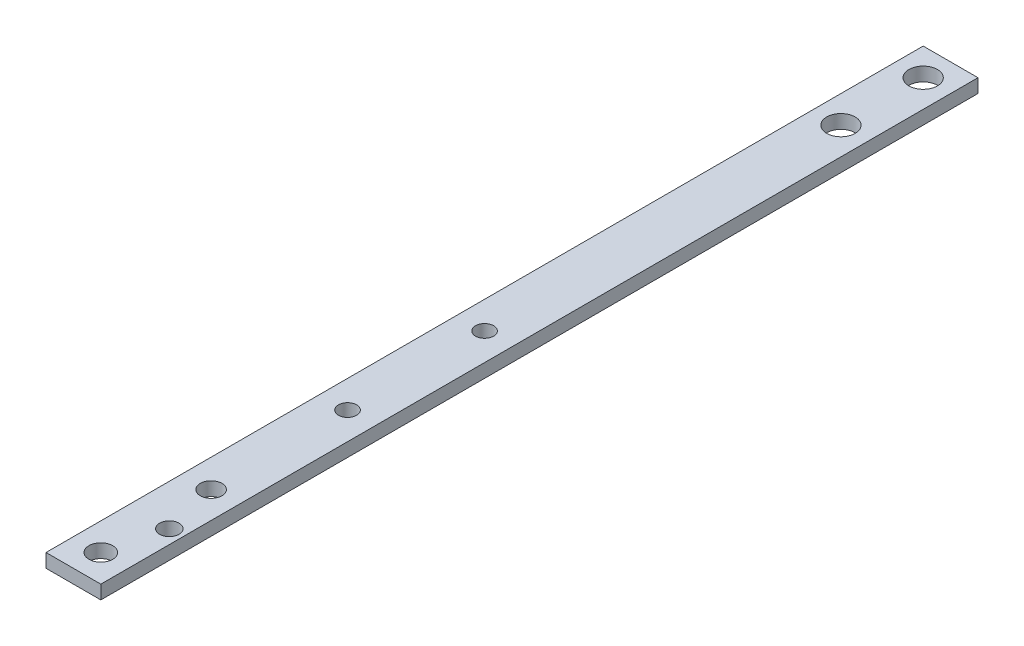
SolidWorks part; units mm, degrees
material "Copper"
ref_plane "Front Plane" through (0, 0, 0) normal (0, 0, 1) x (1, 0, 0)
ref_plane "Top Plane" through (0, 0, 0) normal (0, 1, 0) x (1, 0, 0)
ref_plane "Right Plane" through (0, 0, 0) normal (1, 0, 0) x (0, 0, -1)
sketch "Sketch1" plane through (0, 0, 0) normal (0, 0, 1) x (1, 0, 0)
  line L1 (0, 0) -> (12.7, 0)
  line L2 (0, 0) -> (0, 3.175)
  line L3 (0, 3.175) -> (12.7, 3.175)
  line L4 (12.7, 0) -> (12.7, 3.175)
  dimension "D1" = 12.7
  dimension "D2" = 3.175
extrude "Boss-Extrude1" add sketch "Sketch1" along normal blind 203.2
hole_wizard "M6 Clearance Hole1" positions "Sketch3" profile "Sketch2" hole size "M6" standard "ANSI Metric" end condition through all
sketch "Sketch3" plane through (0, 0, 0) normal (0, -1, 0) x (-1, 0, 0)
  line L0 (0, 0) -> (-12.7, 0) construction
  point P0 (-6.35, -6.35)
  point P5 (-6.35, 0)
  point P6 (-6.35, -25.4)
  dimension "D1" = 6.35
  dimension "D2" = 19.05
sketch "Sketch2" plane through (6.35, 0, 6.35) normal (1, 0, 0) x (0, 0, -1)
  line L0 (0, 0) -> (0, 3.175)
  line L1 (0, 3.175) -> (3.3, 3.175)
  line L2 (3.3, 3.175) -> (3.3, 0)
  line L5 (3.3, 0) -> (0, 0)
  line L11 (0, -6.35) -> (0, 107.95) construction
  dimension "Thru Hole Dia." = 6.6
  dimension "Thru Hole Depth" = 3.175
hole_wizard "M5x0.8 Tapped Hole1" positions "Sketch5" profile "Sketch4" tap size "M5x0.8" standard "ANSI Metric" end condition through all
sketch "Sketch5" plane through (0, 0, 0) normal (0, -1, 0) x (-1, 0, 0)
  line L0 (0, -203.2) -> (-12.7, -203.2) construction
  line L1 (28.575, -152.4) -> (-22.225, -152.4) construction
  point P0 (-6.35, -139.7)
  point P2 (-6.35, -107.95)
  point P7 (-6.35, -203.2)
  dimension "D1" = 12.7
  dimension "D2" = 31.75
sketch "Sketch4" plane through (6.35, 0, 139.7) normal (1, 0, 0) x (0, 0, -1)
  line L0 (0, 0) -> (0, 3.175)
  line L1 (0, 3.175) -> (2.1, 3.175)
  line L2 (2.1, 3.175) -> (2.1, 0)
  line L5 (2.1, 0) -> (0, 0)
  line L11 (0, -6.35) -> (0, 107.95) construction
  dimension "Thread Major Dia." = 4.2
  dimension "Thru Tap Drill Depth" = 3.175
hole_wizard "M6x1.0 Tapped Hole1" positions "Sketch7" profile "Sketch6" tap size "M6x1.0" standard "ANSI Metric" end condition through all
sketch "Sketch7" plane through (0, 3.175, 0) normal (0, 1, 0) x (1, 0, 0)
  point P0 (6.5067, -171.45)
sketch "Sketch6" plane through (6.5067, 3.175, 171.45) normal (1, 0, 0) x (0, 0, 1)
  line L0 (0, 0) -> (0, 3.175)
  line L1 (0, 3.175) -> (2.5, 3.175)
  line L2 (2.5, 3.175) -> (2.5, 0)
  line L5 (2.5, 0) -> (0, 0)
  line L11 (0, -6.35) -> (0, 107.95) construction
  dimension "Thread Major Dia." = 5
  dimension "Thru Tap Drill Depth" = 3.175
hole_wizard "M5 Clearance Hole1" positions "Sketch9" profile "Sketch8" hole size "M5" standard "ANSI Metric" end condition through all
sketch "Sketch9" plane through (0, 3.175, 0) normal (0, 1, 0) x (1, 0, 0)
  line L0 (12.7, -203.2) -> (0, -203.2) construction
  point P0 (6.35, -196.85)
  dimension "D1" = 6.35
sketch "Sketch8" plane through (6.35, 3.175, 196.85) normal (1, 0, 0) x (0, 0, 1)
  line L0 (0, 0) -> (0, 3.175)
  line L1 (0, 3.175) -> (2.75, 3.175)
  line L2 (2.75, 3.175) -> (2.75, 0)
  line L5 (2.75, 0) -> (0, 0)
  line L11 (0, -6.35) -> (0, 107.95) construction
  dimension "Thru Hole Dia." = 5.5
  dimension "Thru Hole Depth" = 3.175
hole_wizard "M4 Clearance Hole1" positions "Sketch11" profile "Sketch10" hole size "M4" standard "ANSI Metric" end condition through all
sketch "Sketch11" plane through (0, 0, 0) normal (0, -1, 0) x (-1, 0, 0)
  circle A0 centre (-9.525, -184.15) radius 1.5875 construction
  point P0 (-9.525, -184.15)
sketch "Sketch10" plane through (9.525, 0, 184.15) normal (1, 0, 0) x (0, 0, -1)
  line L0 (0, 0) -> (0, 3.175)
  line L1 (0, 3.175) -> (2.25, 3.175)
  line L2 (2.25, 3.175) -> (2.25, 0)
  line L5 (2.25, 0) -> (0, 0)
  line L11 (0, -6.35) -> (0, 107.95) construction
  dimension "Thru Hole Dia." = 4.5
  dimension "Thru Hole Depth" = 3.175
